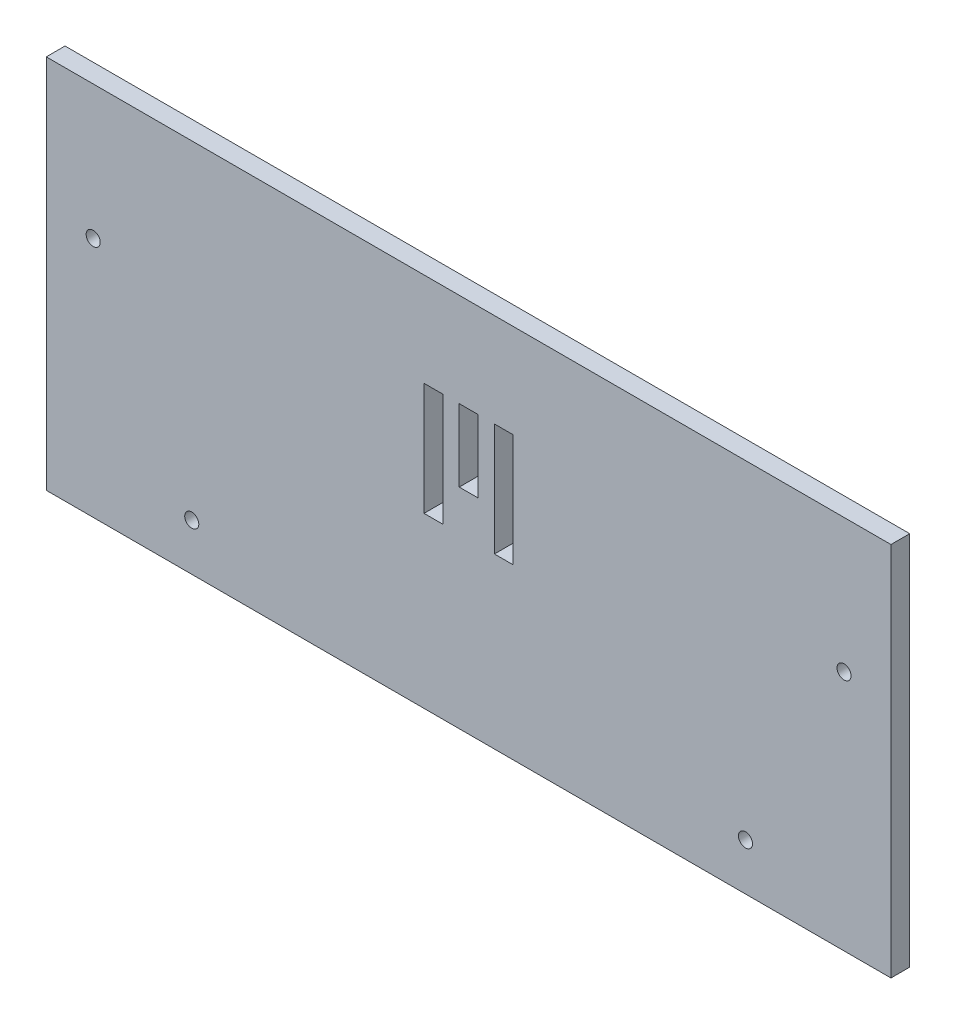
SolidWorks part; units mm, degrees
ref_plane "Front Plane" through (0, 0, 0) normal (0, 0, 1) x (1, 0, 0)
ref_plane "Top Plane" through (0, 0, 0) normal (0, 1, 0) x (1, 0, 0)
ref_plane "Right Plane" through (0, 0, 0) normal (1, 0, 0) x (0, 0, -1)
sketch "Sketch1" plane through (0, 0, 0) normal (0, 0, 1) x (1, 0, 0)
  line L2 (-87.2994, 18.8829) -> (92.7006, 18.8829)
  line L3 (-87.2994, 18.8829) -> (-87.2994, -61.1171)
  line L4 (-87.2994, -61.1171) -> (92.7006, -61.1171)
  line L5 (92.7006, 18.8829) -> (92.7006, -61.1171)
  circle A0 centre (-77.2994, -9.6171) radius 1.5
  circle A1 centre (82.7006, -9.6171) radius 1.5
  circle A2 centre (61.7006, -51.1171) radius 1.5
  circle A3 centre (-56.2994, -51.1171) radius 1.5
  dimension "D1" = 10
  dimension "D10" = 180
  dimension "D2" = 31
  dimension "D3" = 31
  dimension "D4" = 10
  dimension "D5" = 28.5
  dimension "D6" = 28.5
  dimension "D7" = 80
  dimension "D8" = 10
  dimension "D9" = 10
extrude "Boss-Extrude1" add sketch "Sketch1" along normal blind 4
sketch "Sketch2" plane through (0, 0, 4) normal (0, 0, 1) x (1, 0, 0)
  line L1 (-6.7994, -1.1171) -> (-2.7994, -1.1171)
  line L2 (-6.7994, -1.1171) -> (-6.7994, -25.1171)
  line L3 (-6.7994, -25.1171) -> (-2.7994, -25.1171)
  line L4 (-2.7994, -1.1171) -> (-2.7994, -25.1171)
  line L5 (0.7006, -1.1171) -> (4.7006, -1.1171)
  line L6 (0.7006, -1.1171) -> (0.7006, -16.5171)
  line L7 (0.7006, -16.5171) -> (4.7006, -16.5171)
  line L8 (4.7006, -1.1171) -> (4.7006, -16.5171)
  line L12 (12.2006, -1.1171) -> (12.2006, -25.1171)
  line L13 (8.2006, -1.1171) -> (12.2006, -1.1171)
  line L14 (8.2006, -1.1171) -> (8.2006, -25.1171)
  line L15 (8.2006, -25.1171) -> (12.2006, -25.1171)
  line L16 (92.7006, 18.8829) -> (-87.2994, 18.8829) construction
  dimension "D1" = 20
  dimension "D2" = 2
  dimension "D4" = 20
extrude "Cut-Extrude1" cut sketch "Sketch2" against normal blind 4
